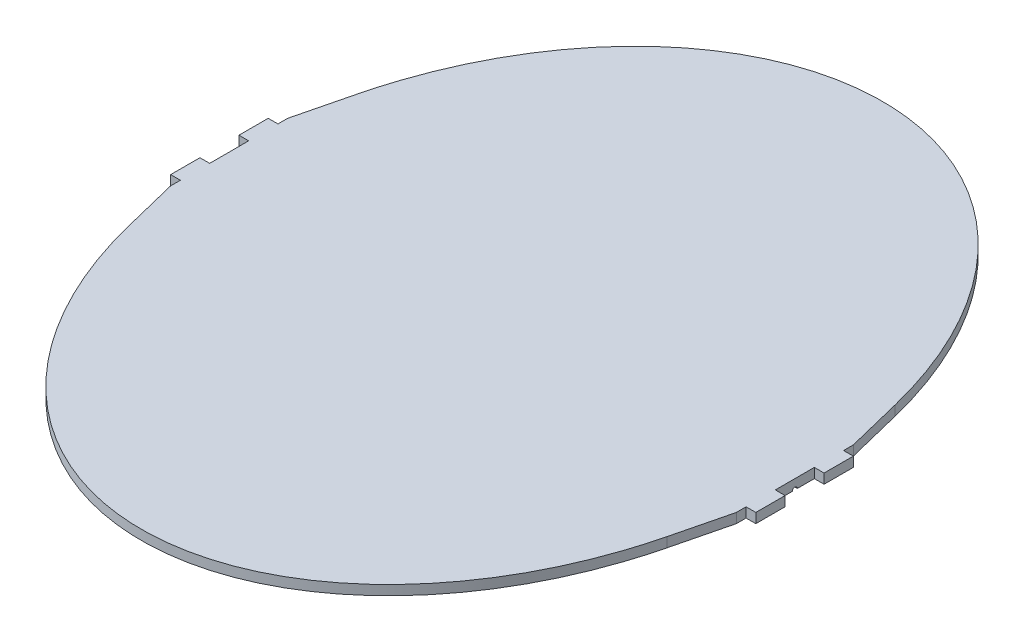
SolidWorks part; units mm, degrees
ref_plane "Front Plane" through (0, 0, 0) normal (0, 0, 1) x (1, 0, 0)
ref_plane "Top Plane" through (0, 0, 0) normal (0, 1, 0) x (1, 0, 0)
ref_plane "Right Plane" through (0, 0, 0) normal (1, 0, 0) x (0, 0, -1)
sketch "Sketch1" plane through (0, 0, 0) normal (0, 1, 0) x (1, 0, 0)
  ellipse E1 centre (0, 0) end of major axis (0, 380) minor radius 290
  dimension "D3" = 580
  dimension "D4" = 760
extrude "Boss-Extrude1" add sketch "Sketch1" along normal blind 10
sketch "Sketch2" plane through (0, 10, 0) normal (0, 1, 0) x (-1, 0, 0)
  line L0 (-275.8919, -117.0811) -> (-290, -60)
  line L1 (-290, -60) -> (-290, -50)
  line L2 (-290, -60) -> (-290, 60) construction
  line L3 (-290, 0) -> (-290, 20)
  line L4 (-290, 60) -> (-275.8919, 117.0811)
  line L5 (-275.8919, 117.0811) -> (-275.8919, -117.0811)
  line L6 (0, 520.3963) -> (0, -482.8995) construction
  line L7 (0, -520.2694) -> (0, 520.3963) construction
  line L8 (275.8919, 117.0811) -> (275.8919, -117.0811)
  line L9 (290, 60) -> (275.8919, 117.0811)
  line L10 (290, 0) -> (290, 20)
  line L11 (290, -60) -> (290, -50)
  line L12 (275.8919, -117.0811) -> (290, -60)
  line L13 (290, 50) -> (300, 50)
  line L14 (300, 50) -> (300, 20)
  line L15 (300, 20) -> (290, 20)
  line L16 (300, 20) -> (290, 20) construction
  line L17 (290, -20) -> (300, -20)
  line L18 (290, -20) -> (300, -20) construction
  line L19 (300, -20) -> (300, -50)
  line L20 (300, -50) -> (290, -50)
  line L21 (290, -20) -> (290, 0)
  line L22 (290, 50) -> (290, 60)
  line L23 (-290, -20) -> (-300, -20)
  line L24 (-300, -20) -> (-300, -50)
  line L25 (-300, -50) -> (-290, -50)
  line L26 (-290, -20) -> (-290, 0)
  line L27 (-290, 50) -> (-300, 50)
  line L28 (-300, 50) -> (-300, 20)
  line L29 (-300, 20) -> (-290, 20)
  line L30 (-290, 50) -> (-290, 60)
extrude "Boss-Extrude2" add sketch "Sketch2" against normal blind 10
sketch "Sketch3" plane through (290, 0, 0) normal (1, 0, 0) x (0, 0, -1)
  line L0 (-2.5, 0) -> (2.5, 0)
  arc A0 (2.5, 0) -> (-2.5, 0) centre (0, 0) ccw
  dimension "D1" = 5
extrude "Cut-Extrude1" cut sketch "Sketch3" against normal blind 10
sketch "Sketch4" plane through (-290, 0, 0) normal (-1, 0, 0) x (0, 0, 1)
  line L0 (-60, 0) -> (-50, 0) construction
  line L1 (-57.5, 0) -> (-52.5, 0)
  circle A0 centre (-55, 0) radius 2.5 construction
  arc A1 (-52.5, 0) -> (-57.5, 0) centre (-55, 0) ccw
  dimension "D1" = 5
extrude "Cut-Extrude2" cut sketch "Sketch4" against normal blind 10
